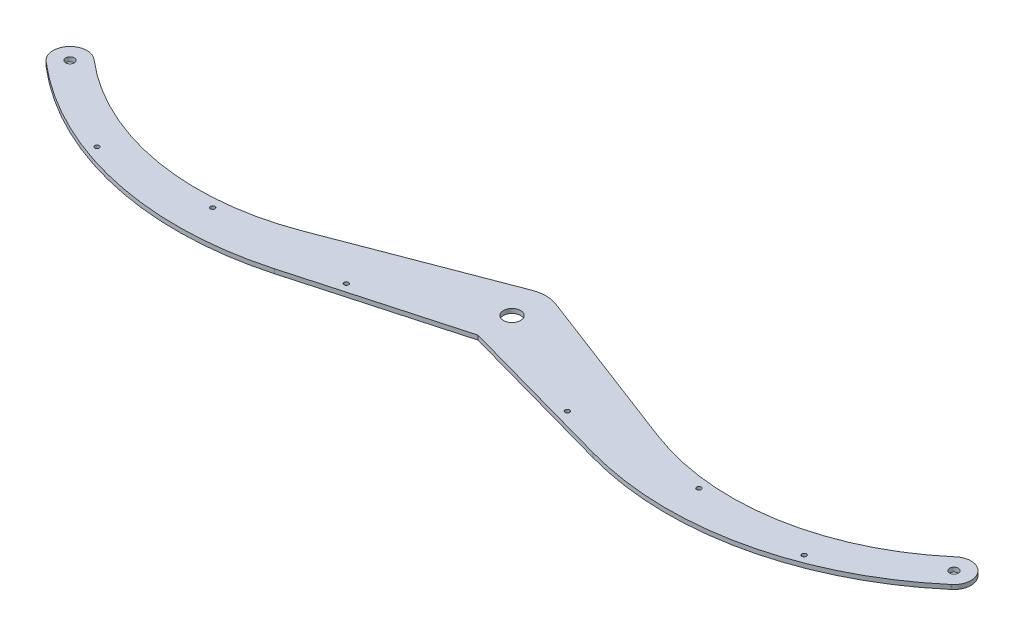
SolidWorks part; units mm, degrees
ref_plane "Front Plane" through (0, 0, 0) normal (0, 0, 1) x (1, 0, 0)
ref_plane "Top Plane" through (0, 0, 0) normal (0, 1, 0) x (1, 0, 0)
ref_plane "Right Plane" through (0, 0, 0) normal (1, 0, 0) x (0, 0, -1)
sketch "Sketch1" plane through (0, 0, 0) normal (0, 1, 0) x (1, 0, 0)
  line L0 (0, 0) -> (-325, 0) construction
  line L1 (-316.8833, 9.5062) -> (-316.4574, 9.1426)
  line L2 (-130.353, -23.0003) -> (-8.9158, 23.3561)
  line L3 (-333.1167, -9.5062) -> (-332.6908, -9.8699)
  line L4 (-117.1576, -57.5674) -> (0, -25)
  line L5 (-316.4574, 9.1426) -> (-332.6908, -9.8699) construction
  line L6 (-130.353, -23.0003) -> (-117.1576, -57.5674) construction
  line L7 (0, -25) -> (0, 25) construction
  line L8 (117.1576, -57.5674) -> (0, -25)
  line L9 (130.353, -23.0003) -> (8.9158, 23.3561)
  line L10 (333.1167, -9.5062) -> (332.6908, -9.8699)
  line L11 (316.8833, 9.5062) -> (316.4574, 9.1426)
  arc A0 (8.9158, 23.3561) -> (-8.9158, 23.3561) centre (0, 0) ccw
  arc A1 (-316.8833, 9.5062) -> (-333.1167, -9.5062) centre (-325, 0) ccw
  arc A2 (-316.4574, 9.1426) -> (-130.353, -23.0003) centre (-196.3298, 149.835) ccw
  arc A3 (-332.6908, -9.8699) -> (-117.1576, -57.5674) centre (-180.0963, 168.8475) ccw
  arc A4 (332.6908, -9.8699) -> (117.1576, -57.5674) centre (180.0963, 168.8475) cw
  arc A5 (316.4574, 9.1426) -> (130.353, -23.0003) centre (196.3298, 149.835) cw
  arc A6 (316.8833, 9.5062) -> (333.1167, -9.5062) centre (325, 0) cw
  dimension "D3" = 25
  dimension "D6" = 235
  dimension "D7" = 185
  dimension "D1" = 25
  dimension "Half of Chassis Width" = 325
  dimension "D4" = 25
  dimension "D5" = 37
  dimension "D8" = 50
extrude "Boss-Extrude1" add sketch "Sketch1" along normal blind 3.18
sketch "Sketch3" plane through (0, 3.18, 0) normal (0, 1, 0) x (1, 0, 0)
  line L0 (0, 25) -> (0, -25) construction
  line L1 (-325, 0) -> (0, 0) construction
  line L2 (-260, 0) -> (-260, -52.1511) construction
  line L3 (-178.75, 0) -> (-178.75, -34.3278) construction
  line L4 (-81.25, 0) -> (-81.25, -47.5858) construction
  line L5 (-117.1576, -57.5674) -> (0, -25) construction
  circle A0 centre (-325, 0) radius 3.175
  arc A1 (8.9158, 23.3561) -> (-8.9158, 23.3561) centre (0, 0) ccw construction
  circle A13 centre (0, 0) radius 6.35
  circle A14 centre (-260, -45.1511) radius 1.65
  circle A19 centre (-178.75, -41.3278) radius 1.65
  circle A20 centre (-81.25, -40.5858) radius 1.65
  arc A21 (-332.6908, -9.8699) -> (-117.1576, -57.5674) centre (-180.0963, 168.8475) ccw construction
  arc A22 (-316.4574, 9.1426) -> (-130.353, -23.0003) centre (-196.3298, 149.835) ccw construction
  circle A23 centre (81.25, -40.5858) radius 1.65
  circle A24 centre (178.75, -41.3278) radius 1.65
  circle A25 centre (260, -45.1511) radius 1.65
  circle A26 centre (325, 0) radius 3.175
  dimension "D1" = 6.35
  dimension "D3" = 12.7
  dimension "D2" = 3.3
  dimension "Hole3" = 260
  dimension "Hole1" = 81.25
  dimension "D7" = 7
  dimension "D5" = 7
  dimension "D8" = 7
  dimension "Hole2" = 178.75
extrude "Cut-Extrude1" cut sketch "Sketch3" against normal through all
equation "\"Half of Chassis Width@Sketch1\"= \"Chassis Width@Differential System Assy - Option 3.Assembly\" / 2"
equation "\"Hole3@Sketch3\"= \"Chassis Width@Differential System Assy - Option 3.Assembly\" * ( 8 / 10 ) / 2"
equation "\"Hole2@Sketch3\" = \"Chassis Width@Differential System Assy - Option 3.Assembly\" / 2 * ( 0.55 )"
equation "\"Hole1@Sketch3\"= \"Chassis Width@Differential System Assy - Option 3.Assembly\" / 2 * 0.25"
